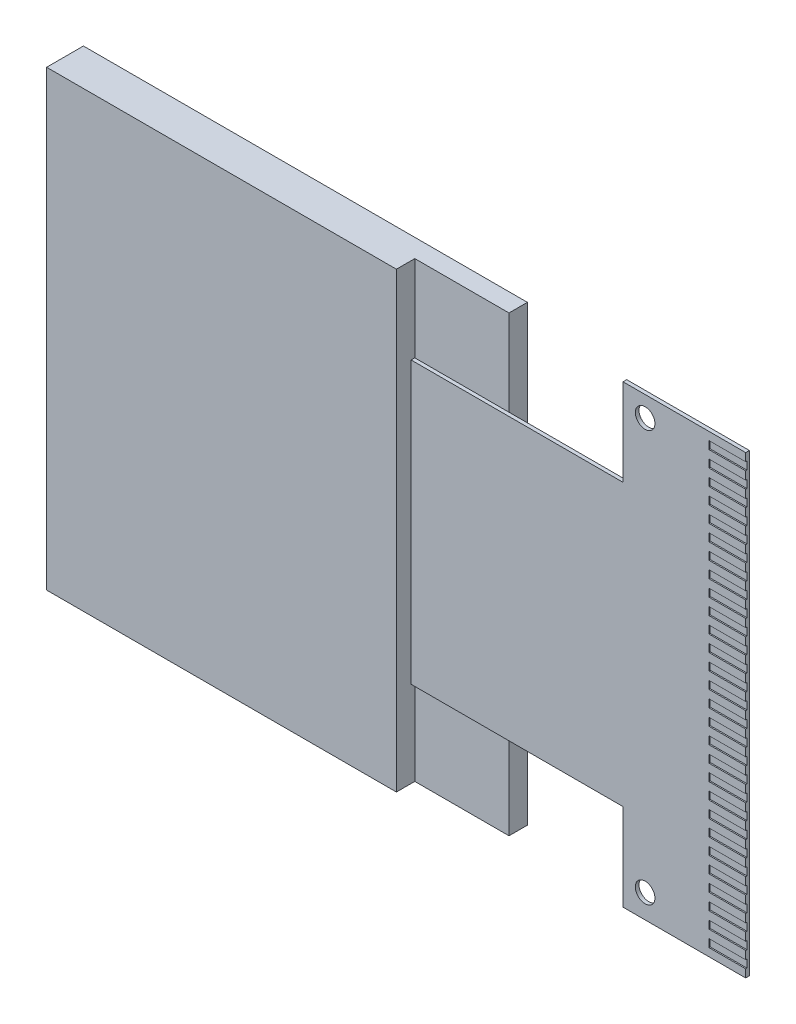
SolidWorks part; units mm, degrees
ref_plane "Front Plane" through (0, 0, 0) normal (0, 0, 1) x (1, 0, 0)
ref_plane "Top Plane" through (0, 0, 0) normal (0, 1, 0) x (1, 0, 0)
ref_plane "Right Plane" through (0, 0, 0) normal (1, 0, 0) x (0, 0, -1)
sketch "Sketch1" plane through (0, 0, 0) normal (0, 0, 1) x (1, 0, 0)
  line L1 (0, 0) -> (18.1, 0)
  line L2 (0, 0) -> (0, 18.46)
  line L3 (0, 18.46) -> (18.1, 18.46)
  line L4 (18.1, 0) -> (18.1, 18.46)
  dimension "D1" = 18.46
  dimension "D2" = 18.1
extrude "Boss-Extrude1" add sketch "Sketch1" along normal blind 1.5
sketch "Sketch2" plane through (0, 0, 1.5) normal (0, 0, 1) x (1, 0, 0)
  line L0 (0, 0) -> (18.1, 0) construction
  line L1 (18.1, 18.46) -> (14.26, 18.46)
  line L2 (18.1, 18.46) -> (18.1, 0)
  line L3 (18.1, 0) -> (14.26, 0)
  line L4 (14.26, 18.46) -> (14.26, 0)
  line L5 (0, 18.46) -> (0, 0) construction
  dimension "D1" = 14.26
extrude "Cut-Extrude1" cut sketch "Sketch2" against normal blind 0.75
sketch "Sketch3" plane through (0, 0, 0.75) normal (0, 0, 1) x (1, 0, 0)
  line L0 (14.26, 18.46) -> (14.26, 0) construction
  line L1 (22.9, 18.505) -> (27.9, 18.505)
  line L2 (14.26, 14.955) -> (14.26, 3.505)
  line L3 (22.9, -0.045) -> (27.9, -0.045)
  line L4 (27.9, 18.505) -> (27.9, -0.045)
  line L6 (27.9, 9.23) -> (0, 9.23) construction
  line L7 (14.26, 14.955) -> (22.9, 14.955)
  line L8 (22.9, 18.505) -> (22.9, 14.955)
  line L9 (18.1, 0) -> (18.1, 18.46) construction
  line L10 (0, 18.46) -> (0, 0) construction
  line L11 (14.26, 3.505) -> (22.9, 3.505)
  line L12 (22.9, -0.045) -> (22.9, 3.505)
  point P18 (0, 9.23)
  dimension "D1" = 9.8
  dimension "D2" = 5
  dimension "D3" = 18.55
  dimension "D4" = 3.55
extrude "Boss-Extrude2" add sketch "Sketch3" along normal blind 0.15 separate body
sketch "Sketch4" plane through (0, 0, 0.9) normal (0, 0, 1) x (1, 0, 0)
  line L2 (27.9, -0.045) -> (27.9, 18.505) construction
  circle A0 centre (23.8, 17.675) radius 0.4
  circle A1 centre (23.8, 0.925) radius 0.4
  dimension "D1" = 0.8
  dimension "D2" = 16.75
  dimension "D3" = 4.1
extrude "Cut-Extrude2" cut sketch "Sketch4" against normal up to next (0.15 mm away)
sketch "Sketch5" plane through (0, 0, 0.9) normal (0, 0, 1) x (1, 0, 0)
  line L0 (27.9, -0.045) -> (27.9, 18.505) construction
  line L1 (27.9, 0.2787) -> (26.4, 0.2787)
  line L2 (27.9, 0.5987) -> (27.9, 0.2787)
  line L3 (27.9, 0.5987) -> (26.4, 0.5987)
  line L4 (26.4, 0.2787) -> (26.4, 0.5987)
  line L5 (26.4, 0.4387) -> (27.9, 0.4387) construction
  line L6 (27.9, 0.9299) -> (26.4, 0.9299)
  line L7 (27.9, 1.2499) -> (27.9, 0.9299)
  line L8 (27.9, 1.2499) -> (26.4, 1.2499)
  line L9 (26.4, 0.9299) -> (26.4, 1.2499)
  line L10 (26.4, 1.0899) -> (27.9, 1.0899) construction
  line L11 (27.9, 1.5811) -> (26.4, 1.5811)
  line L12 (27.9, 1.9011) -> (27.9, 1.5811)
  line L13 (27.9, 1.9011) -> (26.4, 1.9011)
  line L14 (26.4, 1.5811) -> (26.4, 1.9011)
  line L15 (26.4, 1.7411) -> (27.9, 1.7411) construction
  line L16 (27.9, 2.2323) -> (26.4, 2.2323)
  line L17 (27.9, 2.5523) -> (27.9, 2.2323)
  line L18 (27.9, 2.5523) -> (26.4, 2.5523)
  line L19 (26.4, 2.2323) -> (26.4, 2.5523)
  line L20 (26.4, 2.3923) -> (27.9, 2.3923) construction
  line L21 (27.9, 2.8835) -> (26.4, 2.8835)
  line L22 (27.9, 3.2035) -> (27.9, 2.8835)
  line L23 (27.9, 3.2035) -> (26.4, 3.2035)
  line L24 (26.4, 2.8835) -> (26.4, 3.2035)
  line L25 (26.4, 3.0435) -> (27.9, 3.0435) construction
  line L26 (27.9, 3.5347) -> (26.4, 3.5347)
  line L27 (27.9, 3.8547) -> (27.9, 3.5347)
  line L28 (27.9, 3.8547) -> (26.4, 3.8547)
  line L29 (26.4, 3.5347) -> (26.4, 3.8547)
  line L30 (26.4, 3.6947) -> (27.9, 3.6947) construction
  line L31 (27.9, 4.1859) -> (26.4, 4.1859)
  line L32 (27.9, 4.5059) -> (27.9, 4.1859)
  line L33 (27.9, 4.5059) -> (26.4, 4.5059)
  line L34 (26.4, 4.1859) -> (26.4, 4.5059)
  line L35 (26.4, 4.3459) -> (27.9, 4.3459) construction
  line L36 (27.9, 4.8371) -> (26.4, 4.8371)
  line L37 (27.9, 5.1571) -> (27.9, 4.8371)
  line L38 (27.9, 5.1571) -> (26.4, 5.1571)
  line L39 (26.4, 4.8371) -> (26.4, 5.1571)
  line L40 (26.4, 4.9971) -> (27.9, 4.9971) construction
  line L41 (27.9, 5.4883) -> (26.4, 5.4883)
  line L42 (27.9, 5.8083) -> (27.9, 5.4883)
  line L43 (27.9, 5.8083) -> (26.4, 5.8083)
  line L44 (26.4, 5.4883) -> (26.4, 5.8083)
  line L45 (26.4, 5.6483) -> (27.9, 5.6483) construction
  line L46 (27.9, 6.1396) -> (26.4, 6.1396)
  line L47 (27.9, 6.4596) -> (27.9, 6.1396)
  line L48 (27.9, 6.4596) -> (26.4, 6.4596)
  line L49 (26.4, 6.1396) -> (26.4, 6.4596)
  line L50 (26.4, 6.2996) -> (27.9, 6.2996) construction
  line L51 (27.9, 6.7908) -> (26.4, 6.7908)
  line L52 (27.9, 7.1108) -> (27.9, 6.7908)
  line L53 (27.9, 7.1108) -> (26.4, 7.1108)
  line L54 (26.4, 6.7908) -> (26.4, 7.1108)
  line L55 (26.4, 6.9508) -> (27.9, 6.9508) construction
  line L56 (27.9, 7.442) -> (26.4, 7.442)
  line L57 (27.9, 7.762) -> (27.9, 7.442)
  line L58 (27.9, 7.762) -> (26.4, 7.762)
  line L59 (26.4, 7.442) -> (26.4, 7.762)
  line L60 (26.4, 7.602) -> (27.9, 7.602) construction
  line L61 (27.9, 8.0932) -> (26.4, 8.0932)
  line L62 (27.9, 8.4132) -> (27.9, 8.0932)
  line L63 (27.9, 8.4132) -> (26.4, 8.4132)
  line L64 (26.4, 8.0932) -> (26.4, 8.4132)
  line L65 (26.4, 8.2532) -> (27.9, 8.2532) construction
  line L66 (27.9, 8.7444) -> (26.4, 8.7444)
  line L67 (27.9, 9.0644) -> (27.9, 8.7444)
  line L68 (27.9, 9.0644) -> (26.4, 9.0644)
  line L69 (26.4, 8.7444) -> (26.4, 9.0644)
  line L70 (26.4, 8.9044) -> (27.9, 8.9044) construction
  line L71 (27.9, 9.3956) -> (26.4, 9.3956)
  line L72 (27.9, 9.7156) -> (27.9, 9.3956)
  line L73 (27.9, 9.7156) -> (26.4, 9.7156)
  line L74 (26.4, 9.3956) -> (26.4, 9.7156)
  line L75 (26.4, 9.5556) -> (27.9, 9.5556) construction
  line L76 (27.9, 10.0468) -> (26.4, 10.0468)
  line L77 (27.9, 10.3668) -> (27.9, 10.0468)
  line L78 (27.9, 10.3668) -> (26.4, 10.3668)
  line L79 (26.4, 10.0468) -> (26.4, 10.3668)
  line L80 (26.4, 10.2068) -> (27.9, 10.2068) construction
  line L81 (27.9, 10.698) -> (26.4, 10.698)
  line L82 (27.9, 11.018) -> (27.9, 10.698)
  line L83 (27.9, 11.018) -> (26.4, 11.018)
  line L84 (26.4, 10.698) -> (26.4, 11.018)
  line L85 (26.4, 10.858) -> (27.9, 10.858) construction
  line L86 (27.9, 11.3492) -> (26.4, 11.3492)
  line L87 (27.9, 11.6692) -> (27.9, 11.3492)
  line L88 (27.9, 11.6692) -> (26.4, 11.6692)
  line L89 (26.4, 11.3492) -> (26.4, 11.6692)
  line L90 (26.4, 11.5092) -> (27.9, 11.5092) construction
  line L91 (27.9, 12.0004) -> (26.4, 12.0004)
  line L92 (27.9, 12.3204) -> (27.9, 12.0004)
  line L93 (27.9, 12.3204) -> (26.4, 12.3204)
  line L94 (26.4, 12.0004) -> (26.4, 12.3204)
  line L95 (26.4, 12.1604) -> (27.9, 12.1604) construction
  line L96 (27.9, 12.6517) -> (26.4, 12.6517)
  line L97 (27.9, 12.9717) -> (27.9, 12.6517)
  line L98 (27.9, 12.9717) -> (26.4, 12.9717)
  line L99 (26.4, 12.6517) -> (26.4, 12.9717)
  line L100 (26.4, 12.8117) -> (27.9, 12.8117) construction
  line L101 (27.9, 13.3029) -> (26.4, 13.3029)
  line L102 (27.9, 13.6229) -> (27.9, 13.3029)
  line L103 (27.9, 13.6229) -> (26.4, 13.6229)
  line L104 (26.4, 13.3029) -> (26.4, 13.6229)
  line L105 (26.4, 13.4629) -> (27.9, 13.4629) construction
  line L106 (27.9, 13.9541) -> (26.4, 13.9541)
  line L107 (27.9, 14.2741) -> (27.9, 13.9541)
  line L108 (27.9, 14.2741) -> (26.4, 14.2741)
  line L109 (26.4, 13.9541) -> (26.4, 14.2741)
  line L110 (26.4, 14.1141) -> (27.9, 14.1141) construction
  line L111 (27.9, 14.6053) -> (26.4, 14.6053)
  line L112 (27.9, 14.9253) -> (27.9, 14.6053)
  line L113 (27.9, 14.9253) -> (26.4, 14.9253)
  line L114 (26.4, 14.6053) -> (26.4, 14.9253)
  line L115 (26.4, 14.7653) -> (27.9, 14.7653) construction
  line L116 (27.9, 15.2565) -> (26.4, 15.2565)
  line L117 (27.9, 15.5765) -> (27.9, 15.2565)
  line L118 (27.9, 15.5765) -> (26.4, 15.5765)
  line L119 (26.4, 15.2565) -> (26.4, 15.5765)
  line L120 (26.4, 15.4165) -> (27.9, 15.4165) construction
  line L121 (27.9, 15.9077) -> (26.4, 15.9077)
  line L122 (27.9, 16.2277) -> (27.9, 15.9077)
  line L123 (27.9, 16.2277) -> (26.4, 16.2277)
  line L124 (26.4, 15.9077) -> (26.4, 16.2277)
  line L125 (26.4, 16.0677) -> (27.9, 16.0677) construction
  line L126 (27.9, 16.5589) -> (26.4, 16.5589)
  line L127 (27.9, 16.8789) -> (27.9, 16.5589)
  line L128 (27.9, 16.8789) -> (26.4, 16.8789)
  line L129 (26.4, 16.5589) -> (26.4, 16.8789)
  line L130 (26.4, 16.7189) -> (27.9, 16.7189) construction
  line L131 (27.9, 17.2101) -> (26.4, 17.2101)
  line L132 (27.9, 17.5301) -> (27.9, 17.2101)
  line L133 (27.9, 17.5301) -> (26.4, 17.5301)
  line L134 (26.4, 17.2101) -> (26.4, 17.5301)
  line L135 (26.4, 17.3701) -> (27.9, 17.3701) construction
  line L136 (27.9, 17.8613) -> (26.4, 17.8613)
  line L137 (27.9, 18.1813) -> (27.9, 17.8613)
  line L138 (27.9, 18.1813) -> (26.4, 18.1813)
  line L139 (26.4, 17.8613) -> (26.4, 18.1813)
  line L140 (26.4, 18.0213) -> (27.9, 18.0213) construction
  line L141 (14.26, 9.23) -> (35.1936, 9.23) construction
  line L142 (14.26, 14.955) -> (14.26, 3.505) construction
  line L143 (26.4, 9.0644) -> (26.4, 9.3956) construction
  point P174 (14.26, 9.23)
  point P175 (26.4, 9.23)
  dimension "D1" = 0.32
  dimension "D2" = 1.5
  dimension "D3" = 28
extrude "Cut-Extrude6" cut sketch "Sketch5" against normal blind 0.05
